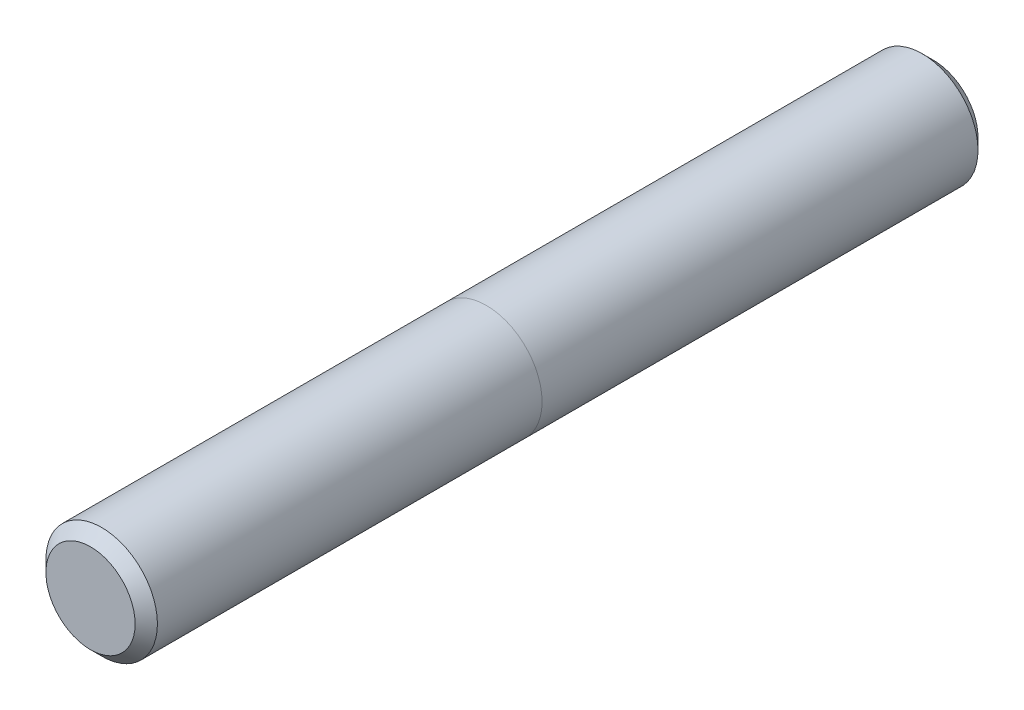
SolidWorks part; units mm, degrees
material "Plain Carbon Steel"
ref_plane "Front" through (0, 0, 0) normal (0, 0, 1) x (1, 0, 0)
ref_plane "Top" through (0, 0, 0) normal (0, 1, 0) x (1, 0, 0)
ref_plane "Right" through (0, 0, 0) normal (1, 0, 0) x (0, 0, -1)
sketch "Sketch1" plane through (0, 0, 0) normal (0, 0, 1) x (1, 0, 0)
  circle A0 centre (0, 0) radius 7.9375
  dimension "Diameter" = 15.875
sketch "Sketch2" plane through (0, 0, 0) normal (1, 0, 0) x (0, 0, -1)
  line L0 (-60, 0) -> (60, 0) construction
  line L1 (-9.2, 7.9375) -> (-9.2, -7.9375) construction
  line L2 (8.7312, 0) -> (-8.7312, 0) construction
  line L3 (9.2, 7.9375) -> (9.2, -7.9375) construction
  line L4 (-60, 7.9375) -> (-60, -7.9375) construction
  line L5 (60, 7.9375) -> (60, -7.9375) construction
  point P3 (-9.2, 0)
  point P8 (0, 0)
  point P9 (9.2, 0)
  point P15 (-60, 0)
  point P18 (60, 0)
  dimension "D1" = 15.875
  dimension "Length" = 120
  dimension "D2" = 50.8
  dimension "D3" = 50.8
sketch "Sketch3" plane through (0, 0, 0) normal (0, 0, 1) x (1, 0, 0)
  circle A0 centre (0, 0) radius 7.9375
  dimension "D1" = 15.875
extrude "Boss-Extrude1" add sketch "Sketch3" along normal mid plane 120
chamfer "Chamfer1" distance 1.5875 angle 45 2 edges at (7.9375, 0, -60) (7.9375, 0, 60)
sketch "Sketch5" plane through (0, 0, 0) normal (0, 1, 0) x (1, 0, 0)
  line L0 (-7.9375, -3.65) -> (7.9375, -3.65)
  line L1 (-7.9375, 58.4125) -> (-7.9375, -58.4125) construction
  line L2 (7.9375, -58.4125) -> (7.9375, 58.4125) construction
  line L4 (-6.35, -60) -> (6.35, -60) construction
  dimension "D1" = 56.35
split line "Split Line1"
equation "\"D1@Sketch3\" = \"Diameter@Sketch1\""
equation "\"D1@Boss-Extrude1\" = \"Length@Sketch2\""
equation "\"D1@Chamfer1\" = \"Diameter@Sketch1\" * .1"
equation "\"D1@Sketch2\" = \"Diameter@Sketch1\""
